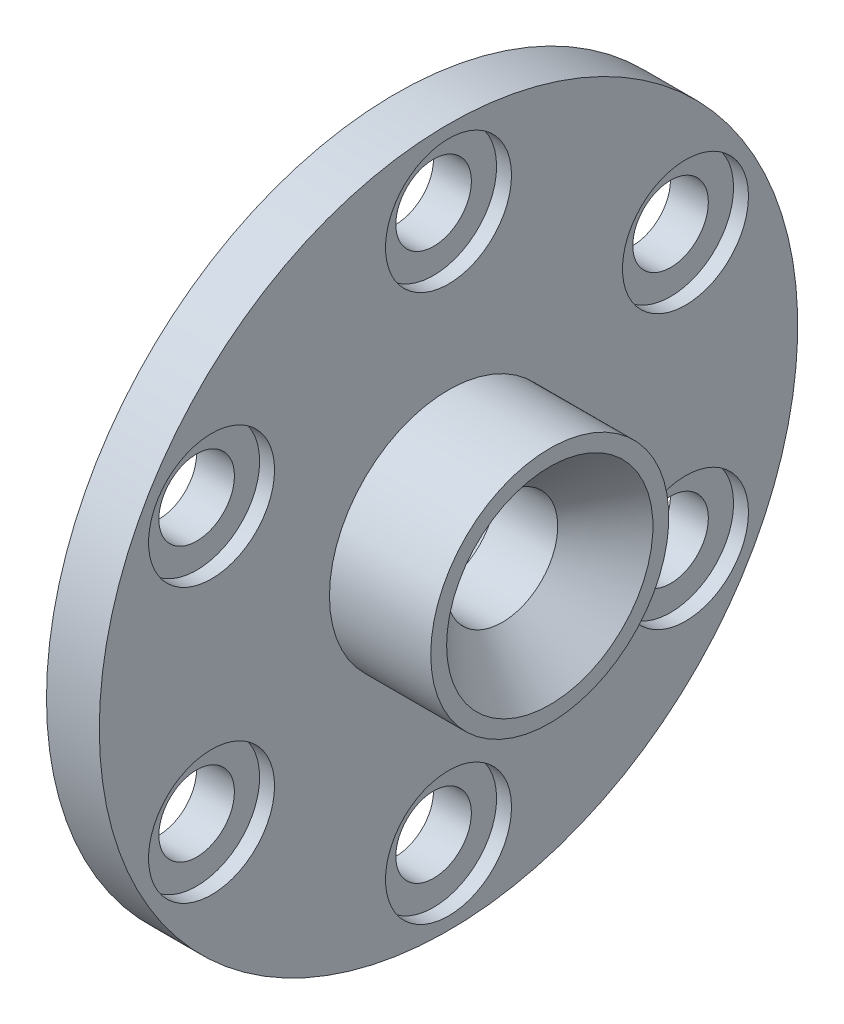
SolidWorks part; units mm, degrees
ref_plane "Front Plane" through (0, 0, 0) normal (0, 0, 1) x (1, 0, 0)
ref_plane "Top Plane" through (0, 0, 0) normal (0, 1, 0) x (1, 0, 0)
ref_plane "Right Plane" through (0, 0, 0) normal (1, 0, 0) x (0, 0, -1)
sketch "Sketch2" plane through (0, 0, 0) normal (0, 0, 1) x (1, 0, 0)
  line L0 (0, 0) -> (58.591, 0) construction
  line L2 (0, 0) -> (18.4, 0)
  line L3 (0, 0) -> (0, 2.5)
  line L4 (0, 2.5) -> (18.4, 2.5)
  line L5 (18.4, 0) -> (18.4, 2.5)
  line L6 (6.0094, 2.5) -> (6.0094, 6)
  line L11 (6.0094, 6) -> (9.9794, 6)
  line L16 (12.9794, 6) -> (12.9794, 3)
  line L17 (12.9794, 3) -> (13.6398, 3)
  line L18 (13.6398, 3) -> (13.6398, 2.5)
  line L19 (13.6398, 2.5) -> (6.0094, 2.5)
  line L22 (13.6398, 2.5) -> (16.1198, 2.5)
  line L23 (13.6398, 2.5) -> (13.6398, 4)
  line L24 (13.6398, 4) -> (16.1198, 4)
  line L25 (16.1198, 2.5) -> (16.1198, 4)
  line L27 (6.0094, 6) -> (9.9794, 6)
  line L28 (6.0094, 6) -> (6.0094, 9)
  line L29 (6.0094, 9) -> (9.9794, 9)
  line L30 (9.9794, 6) -> (9.9794, 9)
  line L31 (6.0094, 9) -> (6.0094, 8.25)
  line L32 (6.0094, 8.25) -> (5.0094, 8.25)
  line L33 (8.6609, 22.001) -> (8.6609, 12.476) construction
  line L34 (5.0094, 12.476) -> (12.3124, 12.476)
  line L35 (9.9794, 9) -> (12.3124, 9)
  line L36 (5.0094, 7.9375) -> (1.7709, 7.9375)
  line L37 (5.0094, 8.25) -> (5.0094, 12.476)
  line L38 (5.0094, 7.9375) -> (5.0094, 13.9365)
  line L39 (5.0094, 13.9365) -> (1.7709, 13.9365)
  line L40 (1.7709, 7.9375) -> (1.7709, 13.9365)
  line L41 (5.0094, 22.001) -> (12.3124, 22.001)
  line L42 (5.0094, 22.001) -> (5.0094, 30.1625)
  line L43 (5.0094, 30.1625) -> (12.3124, 30.1625)
  line L44 (12.3124, 22.001) -> (12.3124, 30.1625)
  line L49 (16.6398, 22.001) -> (16.6398, 7.5)
  line L51 (23.0198, 7.5) -> (23.0198, 6.5)
  line L54 (16.1198, 4) -> (13.6398, 4)
  line L56 (18.0398, 7.5) -> (23.0198, 7.5)
  line L57 (13.3124, 22.001) -> (16.6398, 22.001)
  line L58 (16.1198, 3.5) -> (20.0198, 3.5)
  line L59 (29.9098, 14) -> (26.9098, 11)
  line L60 (4.0094, 31.75) -> (18.0398, 31.75)
  line L61 (18.0398, 7.5) -> (23.0198, 7.5)
  line L62 (18.0398, 7.5) -> (18.0398, 12)
  line L63 (18.0398, 12) -> (23.0198, 12)
  line L64 (23.0198, 7.5) -> (23.0198, 12)
  line L65 (18.0398, 31.75) -> (18.0398, 12)
  line L66 (23.0198, 11) -> (26.9098, 11)
  line L67 (34.8098, 23) -> (31.3098, 19.5)
  line L68 (35.8098, 31) -> (38.7998, 33.99)
  line L69 (29.9098, 14) -> (29.9098, 15)
  line L70 (29.9098, 15) -> (22.9398, 15)
  line L71 (22.9398, 15) -> (21.0398, 15)
  line L72 (18.0398, 7.5) -> (16.6398, 7.5)
  line L73 (21.0398, 15) -> (21.0398, 43)
  line L74 (19.6115, 40) -> (9.6516, 40)
  line L75 (9.6516, 40) -> (4.0094, 40)
  line L76 (21.0398, 43) -> (19.6115, 43)
  line L77 (22.9398, 15) -> (29.9098, 15)
  line L78 (22.9398, 15) -> (22.9398, 21)
  line L79 (22.9398, 21) -> (29.9098, 21)
  line L80 (29.9098, 15) -> (29.9098, 21)
  line L81 (9.6516, 40) -> (19.6115, 40)
  line L82 (9.6516, 40) -> (9.6516, 50)
  line L83 (9.6516, 50) -> (19.6115, 50)
  line L84 (19.6115, 40) -> (19.6115, 50)
  line L85 (4.0094, 40) -> (4.0094, 31.75)
  line L86 (12.9794, 3) -> (12.9794, 2.5)
  line L87 (31.3098, 19.5) -> (29.9098, 19.5)
  line L88 (21.4694, 63.5) -> (21.4694, 51.308)
  line L89 (21.4694, 63.5) -> (25.9398, 63.5)
  line L90 (25.9398, 63.5) -> (25.9398, 25)
  line L91 (27.8398, 25) -> (25.9398, 25)
  line L92 (9.6516, 48) -> (8.2233, 48)
  line L93 (8.2233, 48) -> (8.2233, 53.476)
  line L94 (8.2233, 53.476) -> (19.6115, 53.476)
  line L95 (19.6115, 53.476) -> (19.6115, 50)
  line L96 (13.9174, 63.001) -> (13.9174, 53.476) construction
  line L97 (8.2233, 63.001) -> (19.6115, 63.001)
  line L98 (8.2233, 63.001) -> (8.2233, 68.2625)
  line L99 (8.2233, 68.2625) -> (19.6115, 68.2625)
  line L100 (19.6115, 63.001) -> (19.6115, 68.2625)
  line L101 (12.9794, 6) -> (11.9794, 6)
  line L102 (8.2233, 44.825) -> (4.9848, 44.825)
  line L103 (8.2233, 44.825) -> (8.2233, 54.9365)
  line L104 (8.2233, 54.9365) -> (4.9848, 54.9365)
  line L106 (9.9794, 6) -> (10.8794, 6)
  line L107 (27.8398, 25) -> (34.8098, 25)
  line L108 (34.8098, 25) -> (34.8098, 23)
  line L109 (0, 0) -> (-2, 0)
  line L110 (0, 0) -> (0, 11)
  line L111 (27.8398, 25) -> (34.8098, 25)
  line L112 (27.8398, 25) -> (27.8398, 32.5)
  line L113 (27.8398, 32.5) -> (34.8098, 32.5)
  line L114 (34.8098, 25) -> (34.8098, 32.5)
  line L115 (35.8098, 31) -> (34.8098, 31)
  line L116 (27.8398, 32.5) -> (27.8398, 64.5)
  line L117 (20.5849, 74.025) -> (6.2499, 74.025)
  line L118 (6.2499, 74.025) -> (6.2499, 76.2)
  line L119 (38.7998, 47.29) -> (30.8398, 55.25)
  line L120 (0, 11) -> (-2, 11)
  line L121 (38.7998, 43.815) -> (30.8623, 43.815)
  line L123 (-4.8152, 69.85) -> (1.5348, 76.2)
  line L124 (38.7998, 47.29) -> (38.7998, 33.99)
  line L125 (-2, 0) -> (-2, 11)
  line L126 (38.7998, 37.465) -> (30.8623, 37.465)
  line L127 (30.8623, 43.815) -> (30.8623, 37.465)
  line L128 (6.0094, 2.5) -> (6.0094, 0)
  line L129 (-0.0152, 63.5) -> (-0.0152, 30)
  line L132 (4.9848, 63.5) -> (-0.0152, 63.5)
  line L136 (-1.8152, 30) -> (-11.7752, 30)
  line L138 (-13.7752, 25.4) -> (-2, 25.4)
  line L139 (-2, 25.4) -> (-2, 11.5)
  line L140 (27.8398, 64.5) -> (20.5849, 64.5)
  line L141 (-1.8152, 30) -> (-11.7752, 30)
  line L142 (-1.8152, 30) -> (-1.8152, 39)
  line L143 (-1.8152, 39) -> (-11.7752, 39)
  line L144 (-11.7752, 30) -> (-11.7752, 39)
  line L145 (20.5849, 64.5) -> (20.5849, 74.025)
  line L146 (-12.7752, 37) -> (-12.7752, 47.29)
  line L147 (-12.7752, 37) -> (-11.7752, 37)
  line L148 (30.8398, 55.25) -> (30.8398, 76.2)
  line L149 (11.9794, 6) -> (11.9794, 5.45)
  line L154 (-2, 11.5) -> (0.5, 11.5)
  line L155 (4.9848, 60.6197) -> (24.0348, 60.6197)
  line L160 (4.9848, 60.6197) -> (4.9848, 55.8572)
  line L161 (4.9848, 55.8572) -> (24.0348, 55.8572)
  line L166 (24.0348, 60.6197) -> (24.0348, 55.8572)
  line L167 (4.9848, 60.6197) -> (24.0348, 55.8572) construction
  line L172 (4.9848, 55.8572) -> (24.0348, 60.6197) construction
  line L173 (24.0348, 62.2072) -> (25.9398, 62.2072)
  line L174 (11.9794, 5.45) -> (10.8794, 5.45)
  line L175 (10.8794, 6) -> (10.8794, 5.45)
  line L176 (24.0348, 62.2072) -> (24.0348, 54.2697)
  line L177 (24.0348, 54.2697) -> (25.9398, 54.2697)
  line L178 (25.9398, 62.2072) -> (25.9398, 54.2697)
  line L179 (24.0348, 62.2072) -> (25.9398, 54.2697) construction
  line L180 (24.0348, 54.2697) -> (25.9398, 62.2072) construction
  line L181 (3, 19.6197) -> (15.7, 19.6197)
  line L182 (3, 19.6197) -> (3, 14.8572)
  line L183 (3, 14.8572) -> (15.7, 14.8572)
  line L184 (15.7, 19.6197) -> (15.7, 14.8572)
  line L185 (3, 19.6197) -> (15.7, 14.8572) construction
  line L186 (3, 14.8572) -> (15.7, 19.6197) construction
  line L187 (15.7, 21.2072) -> (16.6398, 21.2072)
  line L188 (15.7, 21.2072) -> (15.7, 13.2697)
  line L189 (15.7, 13.2697) -> (16.6398, 13.2697)
  line L190 (16.6398, 21.2072) -> (16.6398, 13.2697)
  line L191 (15.7, 21.2072) -> (16.6398, 13.2697) construction
  line L192 (15.7, 13.2697) -> (16.6398, 21.2072) construction
  line L193 (0.5, 11.5) -> (0.5, 6.9375)
  line L194 (0.5, 6.9375) -> (1.7709, 6.9375)
  line L195 (23.0198, 6.5) -> (20.0198, 3.5)
  line L196 (4.9848, 63.5) -> (4.9848, 54.9365)
  line L197 (3, 43.825) -> (4.9848, 43.825)
  line L198 (1.7709, 6.9375) -> (1.7709, 7.9375)
  line L199 (6.0094, 0) -> (12.9794, 0)
  line L200 (12.9794, 0) -> (12.9794, 2.5)
  line L201 (18.0398, 31.75) -> (18.0398, 35.875)
  line L202 (18.0398, 35.875) -> (21.0398, 35.875)
  line L203 (30.8398, 76.2) -> (6.2499, 76.2)
  line L204 (2.8049, 69.85) -> (7.2499, 69.85) construction
  line L205 (7.2499, 67.4688) -> (26.2999, 67.4688)
  line L206 (7.2499, 74.025) -> (7.2499, 64.5)
  line L207 (7.2499, 64.5) -> (-1.8152, 64.5)
  line L208 (-1.8152, 64.5) -> (-1.8152, 39)
  line L209 (-12.7752, 47.29) -> (-4.8152, 55.25)
  line L210 (-4.8152, 55.25) -> (-4.8152, 69.85)
  line L211 (7.2499, 67.4688) -> (7.2499, 72.2312)
  line L212 (7.2499, 72.2312) -> (26.2999, 72.2313)
  line L213 (26.2999, 67.4688) -> (26.2999, 72.2313)
  line L214 (26.2999, 73.8187) -> (30.8398, 73.8187)
  line L215 (26.2999, 73.8187) -> (26.2999, 65.8813)
  line L216 (26.2999, 65.8813) -> (30.8398, 65.8813)
  line L217 (30.8398, 73.8187) -> (30.8398, 65.8813)
  line L218 (2.8049, 72.2313) -> (25.0299, 72.2313)
  line L219 (2.8049, 72.2313) -> (2.8049, 67.4687)
  line L220 (2.8049, 67.4687) -> (25.0299, 67.4687)
  line L221 (25.0299, 72.2313) -> (25.0299, 67.4687)
  line L222 (25.0299, 69.85) -> (20.5849, 69.85) construction
  line L223 (21.4694, 51.308) -> (22.9398, 51.308)
  line L224 (22.9398, 51.308) -> (22.9398, 21)
  line L225 (13.6398, 4) -> (13.6398, 12.2697)
  line L226 (13.6398, 12.2697) -> (13.3124, 12.2697)
  line L227 (13.3124, 12.2697) -> (13.3124, 22.001)
  line L228 (12.3124, 9) -> (12.3124, 12.476)
  line L229 (-1.8152, 30) -> (-0.0152, 30)
  line L230 (8.2233, 65.6317) -> (2.8049, 65.6317) construction
  line L231 (19.6115, 65.6317) -> (25.0299, 65.6317) construction
  line L232 (1.5348, 76.2) -> (6.2499, 76.2)
  line L233 (-11.7752, 30) -> (-13.7752, 30)
  line L234 (-13.7752, 30) -> (-13.7752, 25.4)
  line L235 (3, 13.9365) -> (3, 43.825)
  line L236 (4.9848, 54.9365) -> (4.9848, 44.825)
  line L237 (4.9848, 43.825) -> (4.9848, 44.825)
  circle A0 centre (26.8898, 25.95) radius 0.95
  circle A1 centre (21.9898, 15.95) radius 0.95
  circle A2 centre (17.3398, 8.2) radius 0.7
  circle A3 centre (10.4294, 6.45) radius 0.45
  circle A4 centre (-0.9152, 30.9) radius 0.9
  point P7 (24.9873, 58.2385)
  point P131 (16.1699, 17.2385)
  point P135 (14.5098, 58.2385)
  point P146 (9.35, 17.2385)
sketch "Sketch3" plane through (0, 0, 0) normal (0, 0, 1) x (1, 0, 0)
  line L0 (13.3124, 22.001) -> (16.6398, 22.001) construction
  line L1 (16.6398, 22.001) -> (16.6398, 7.5) construction
  line L4 (23.0198, 7.5) -> (23.0198, 6.5) construction
  line L5 (18.0398, 7.5) -> (23.0198, 7.5) construction
  line L7 (13.6398, 4) -> (16.1198, 4) construction
  line L8 (16.1198, 2.5) -> (16.1198, 4) construction
  line L9 (16.1198, 3.5) -> (20.0198, 3.5) construction
  line L10 (23.0198, 6.5) -> (20.0198, 3.5) construction
  line L11 (13.3124, 22.001) -> (16.6398, 22.001)
  line L12 (16.6398, 22.001) -> (16.6398, 7.5)
  line L15 (23.0198, 7.5) -> (23.0198, 6.5)
  line L16 (18.0398, 7.5) -> (23.0198, 7.5)
  line L18 (13.6398, 4) -> (16.1198, 4)
  line L19 (16.1198, 3.5) -> (16.1198, 4)
  line L20 (16.1198, 3.5) -> (20.0198, 3.5)
  line L21 (23.0198, 6.5) -> (20.0198, 3.5)
  line L22 (18.0398, 7.5) -> (16.6398, 7.5) construction
  line L23 (13.6398, 4) -> (13.6398, 12.2697) construction
  line L24 (13.6398, 12.2697) -> (13.3124, 12.2697) construction
  line L25 (13.3124, 12.2697) -> (13.3124, 22.001) construction
  line L26 (18.0398, 7.5) -> (16.6398, 7.5)
  line L27 (13.6398, 4) -> (13.6398, 12.2697)
  line L28 (13.6398, 12.2697) -> (13.3124, 12.2697)
  line L29 (13.3124, 12.2697) -> (13.3124, 22.001)
revolve "Revolve1" add sketch "Sketch3" angle 360 about L0
sketch "Sketch4" plane through (0, 0, 0) normal (1, 0, 0) x (0, 0, -1)
  line L0 (0, 0) -> (0, 69.85) construction
  line L1 (0, 0) -> (13.6271, 68.5079) construction
  line L2 (0, 0) -> (0, 58.2385) construction
  line L3 (0, 0) -> (50.436, 29.1192) construction
  line L4 (0, 0) -> (0, 31.75) construction
  line L5 (0, 0) -> (12.1502, 29.3332) construction
  line L6 (0, 0) -> (0, 17.2385) construction
  line L7 (0, 0) -> (14.929, 8.6192) construction
  line L8 (0, 0) -> (0, 58.2385) construction
  line L9 (0, 0) -> (50.436, 29.1192) construction
  line L10 (0, 0) -> (5.9583, 29.9542) construction
  line L11 (0, 0) -> (16.9677, 25.394) construction
  circle A0 centre (0, 0) radius 69.85 construction
  circle A1 centre (0, 0) radius 58.2385 construction
  circle A2 centre (0, 0) radius 31.75 construction
  circle A3 centre (0, 0) radius 17.2385 construction
  circle A4 centre (0, 69.85) radius 3.175
  circle A5 centre (0, 58.2385) radius 4.7625
  circle A6 centre (0, 31.75) radius 3.175
  circle A7 centre (0, 17.2385) radius 4.7625
  circle A8 centre (13.6271, 68.5079) radius 3.175
  circle A9 centre (26.7304, 64.533) radius 3.175
  circle A10 centre (38.8066, 58.0782) radius 3.175
  circle A11 centre (49.3914, 49.3914) radius 3.175
  circle A12 centre (58.0782, 38.8066) radius 3.175
  circle A13 centre (64.533, 26.7304) radius 3.175
  circle A14 centre (68.5079, 13.6271) radius 3.175
  circle A15 centre (69.85, 0) radius 3.175
  circle A16 centre (68.5079, -13.6271) radius 3.175
  circle A17 centre (64.533, -26.7304) radius 3.175
  circle A18 centre (58.0782, -38.8066) radius 3.175
  circle A19 centre (49.3914, -49.3914) radius 3.175
  circle A20 centre (38.8066, -58.0782) radius 3.175
  circle A21 centre (26.7304, -64.533) radius 3.175
  circle A22 centre (13.6271, -68.5079) radius 3.175
  circle A23 centre (0, -69.85) radius 3.175
  circle A24 centre (-13.6271, -68.5079) radius 3.175
  circle A25 centre (-26.7304, -64.533) radius 3.175
  circle A26 centre (-38.8066, -58.0782) radius 3.175
  circle A27 centre (-49.3914, -49.3914) radius 3.175
  circle A28 centre (-58.0782, -38.8066) radius 3.175
  circle A29 centre (-64.533, -26.7304) radius 3.175
  circle A30 centre (-68.5079, -13.6271) radius 3.175
  circle A31 centre (-69.85, 0) radius 3.175
  circle A32 centre (-68.5079, 13.6271) radius 3.175
  circle A33 centre (-64.533, 26.7304) radius 3.175
  circle A34 centre (-58.0782, 38.8066) radius 3.175
  circle A35 centre (-49.3914, 49.3914) radius 3.175
  circle A36 centre (-38.8066, 58.0782) radius 3.175
  circle A37 centre (-26.7304, 64.533) radius 3.175
  circle A38 centre (-13.6271, 68.5079) radius 3.175
  circle A47 centre (50.436, 29.1192) radius 4.7625
  circle A48 centre (50.436, -29.1192) radius 4.7625
  circle A49 centre (0, -58.2385) radius 4.7625
  circle A50 centre (-50.436, -29.1192) radius 4.7625
  circle A51 centre (-50.436, 29.1192) radius 4.7625
  circle A58 centre (12.1502, 29.3332) radius 3.175
  circle A59 centre (22.4506, 22.4506) radius 3.175
  circle A60 centre (29.3332, 12.1502) radius 3.175
  circle A61 centre (31.75, 0) radius 3.175
  circle A62 centre (29.3332, -12.1502) radius 3.175
  circle A63 centre (22.4506, -22.4506) radius 3.175
  circle A64 centre (12.1502, -29.3332) radius 3.175
  circle A65 centre (0, -31.75) radius 3.175
  circle A66 centre (-12.1502, -29.3332) radius 3.175
  circle A67 centre (-22.4506, -22.4506) radius 3.175
  circle A68 centre (-29.3332, -12.1502) radius 3.175
  circle A69 centre (-31.75, 0) radius 3.175
  circle A70 centre (-29.3332, 12.1502) radius 3.175
  circle A71 centre (-22.4506, 22.4506) radius 3.175
  circle A72 centre (14.929, 8.6192) radius 4.7625
  circle A73 centre (14.929, -8.6192) radius 4.7625
  circle A74 centre (0, -17.2385) radius 4.7625
  circle A75 centre (-14.929, -8.6192) radius 4.7625
  circle A76 centre (-14.929, 8.6192) radius 4.7625
  circle A77 centre (0, 0) radius 50
  circle A78 centre (0, 0) radius 9
  circle A79 centre (-12.1502, 29.3332) radius 3.175
  circle A80 centre (0, 0) radius 76.2
  circle A81 centre (0, 0) radius 74.025
  circle A82 centre (0, 69.85) radius 3.9687
  circle A83 centre (49.3914, 49.3914) radius 3.9687
  circle A84 centre (69.85, 0) radius 3.9688
  circle A85 centre (49.3914, -49.3914) radius 3.9687
  circle A86 centre (0, -69.85) radius 3.9687
  circle A87 centre (-49.3914, -49.3914) radius 3.9687
  circle A88 centre (-69.85, 0) radius 3.9688
  circle A89 centre (-49.3914, 49.3914) radius 3.9687
  circle A90 centre (0, 69.85) radius 2.3812
  circle A91 centre (13.6271, 68.5079) radius 2.3812
  circle A92 centre (26.7304, 64.533) radius 2.3813
  circle A93 centre (38.8066, 58.0782) radius 2.3812
  circle A94 centre (49.3914, 49.3914) radius 2.3812
  circle A95 centre (58.0782, 38.8066) radius 2.3812
  circle A96 centre (64.533, 26.7304) radius 2.3813
  circle A97 centre (68.5079, 13.6271) radius 2.3813
  circle A98 centre (69.85, 0) radius 2.3813
  circle A99 centre (68.5079, -13.6271) radius 2.3813
  circle A100 centre (64.533, -26.7304) radius 2.3813
  circle A101 centre (58.0782, -38.8066) radius 2.3812
  circle A102 centre (49.3914, -49.3914) radius 2.3812
  circle A103 centre (38.8066, -58.0782) radius 2.3812
  circle A104 centre (26.7304, -64.533) radius 2.3813
  circle A105 centre (13.6271, -68.5079) radius 2.3812
  circle A106 centre (0, -69.85) radius 2.3812
  circle A107 centre (-13.6271, -68.5079) radius 2.3812
  circle A108 centre (-26.7304, -64.533) radius 2.3813
  circle A109 centre (-38.8066, -58.0782) radius 2.3812
  circle A110 centre (-49.3914, -49.3914) radius 2.3812
  circle A111 centre (-58.0782, -38.8066) radius 2.3812
  circle A112 centre (-64.533, -26.7304) radius 2.3812
  arc A113 (3.0399, 30.8338) -> (8.9911, 29.65) centre (5.9583, 29.9542) cw
  arc A114 (14.6081, 27.3234) -> (19.6532, 23.9523) centre (16.9677, 25.394) cw
  arc A115 (23.9523, 19.6532) -> (27.3234, 14.6081) centre (25.394, 16.9677) cw
  arc A116 (29.65, 8.9911) -> (30.8338, 3.0399) centre (29.9542, 5.9583) cw
  arc A117 (30.8338, -3.0399) -> (29.65, -8.9911) centre (29.9542, -5.9583) cw
  arc A118 (27.3234, -14.6081) -> (23.9523, -19.6532) centre (25.394, -16.9677) cw
  arc A119 (19.6532, -23.9523) -> (14.6081, -27.3234) centre (16.9677, -25.394) cw
  arc A120 (8.9911, -29.65) -> (3.0399, -30.8338) centre (5.9583, -29.9542) cw
  arc A121 (-3.0399, -30.8338) -> (-8.9911, -29.65) centre (-5.9583, -29.9542) cw
  arc A122 (-14.6081, -27.3234) -> (-19.6532, -23.9523) centre (-16.9677, -25.394) cw
  arc A123 (-23.9523, -19.6532) -> (-27.3234, -14.6081) centre (-25.394, -16.9677) cw
  arc A124 (-29.65, -8.9911) -> (-30.8338, -3.0399) centre (-29.9542, -5.9583) cw
  arc A125 (-30.8338, 3.0399) -> (-29.65, 8.9911) centre (-29.9542, 5.9583) cw
  arc A126 (-27.3234, 14.6081) -> (-23.9523, 19.6532) centre (-25.394, 16.9677) cw
  arc A127 (-19.6532, 23.9523) -> (-14.6081, 27.3234) centre (-16.9677, 25.394) cw
  arc A128 (-8.9911, 29.65) -> (-3.0399, 30.8338) centre (-5.9583, 29.9542) cw
  arc A129 (26.9875, 0) -> (26.9932, 0.1932) centre (30.2705, 0) cw
  arc A130 (65.0988, 0.2771) -> (65.0875, 0) centre (68.4964, 0) ccw
  circle A131 centre (1.5875, 0) radius 40
  circle A132 centre (1.5875, 0) radius 2.5
  circle A133 centre (1.5875, 0) radius 3
  circle A134 centre (1.5875, 0) radius 43
  circle A135 centre (-68.5079, -13.6271) radius 2.3813
  circle A136 centre (-69.85, 0) radius 2.3813
  circle A137 centre (-68.5079, 13.6271) radius 2.3813
  circle A138 centre (-64.533, 26.7304) radius 2.3812
  circle A139 centre (-58.0782, 38.8066) radius 2.3812
  circle A140 centre (-49.3914, 49.3914) radius 2.3812
  circle A141 centre (-38.8066, 58.0782) radius 2.3812
  circle A142 centre (-26.7304, 64.533) radius 2.3813
  circle A143 centre (-13.6271, 68.5079) radius 2.3812
  circle A144 centre (0, 58.2385) radius 2.3812
  circle A145 centre (0, 58.2385) radius 3.9688
  circle A146 centre (50.436, 29.1192) radius 3.9688
  circle A147 centre (50.436, 29.1192) radius 2.3813
  circle A148 centre (50.436, -29.1192) radius 3.9687
  circle A149 centre (50.436, -29.1192) radius 2.3812
  circle A150 centre (0, -58.2385) radius 3.9687
  circle A151 centre (0, -58.2385) radius 2.3812
  circle A152 centre (-50.436, -29.1192) radius 3.9687
  circle A153 centre (-50.436, -29.1192) radius 2.3812
  circle A154 centre (-50.436, 29.1192) radius 3.9687
  circle A155 centre (-50.436, 29.1192) radius 2.3812
  spline S1 degree 4 number of poles 499 (26.9875, 0) -> (26.9932, 0.1932)
  spline S3 degree 4 number of poles 617 (65.0875, 0) -> (65.0988, 0.2771)
  point P116 (0, 0)
  point P225 (0, 0)
sketch "Sketch5" plane through (0, 0, 0) normal (1, 0, 0) x (0, 0, -1)
  circle A0 centre (-14.929, 8.6192) radius 4.7625 construction
  circle A1 centre (-14.929, -8.6192) radius 4.7625 construction
  circle A2 centre (0, -17.2385) radius 4.7625 construction
  circle A3 centre (14.929, -8.6192) radius 4.7625 construction
  circle A4 centre (14.929, 8.6192) radius 4.7625 construction
  circle A5 centre (0, 17.2385) radius 4.7625 construction
  circle A6 centre (-14.929, 8.6192) radius 4.7625
  circle A7 centre (-14.929, -8.6192) radius 4.7625
  circle A8 centre (0, -17.2385) radius 4.7625
  circle A9 centre (14.929, -8.6192) radius 4.7625
  circle A10 centre (14.929, 8.6192) radius 4.7625
  circle A11 centre (0, 17.2385) radius 4.7625
  circle A12 centre (0, 17.2385) radius 2.3813
  circle A13 centre (14.929, 8.6192) radius 2.3813
  circle A14 centre (14.929, -8.6192) radius 2.3813
  circle A15 centre (0, -17.2385) radius 2.3813
  circle A16 centre (-14.929, -8.6192) radius 2.3813
  circle A17 centre (-14.929, 8.6192) radius 2.3813
  dimension "D1" = 4.7625
extrude "Cut-Extrude1" cut sketch "Sketch5" along normal through all contours A17 | A12 | A13 | A14 | A15 | A16
sketch "Sketch6" plane through (16.6398, 0, 0) normal (1, 0, 0) x (0, 0, -1)
  circle A0 centre (0, 17.2385) radius 3.9688
  circle A1 centre (14.929, 8.6192) radius 3.9688
  circle A2 centre (14.929, -8.6192) radius 3.9687
  circle A3 centre (0, -17.2385) radius 3.9688
  circle A4 centre (-14.929, -8.6192) radius 3.9687
  circle A5 centre (-14.929, 8.6192) radius 3.9687
  dimension "D1" = 7.9375
extrude "Cut-Extrude2" cut sketch "Sketch6" against normal up to vertex (0.9398 mm away) up to point (15.7, 21.2072, 0)
